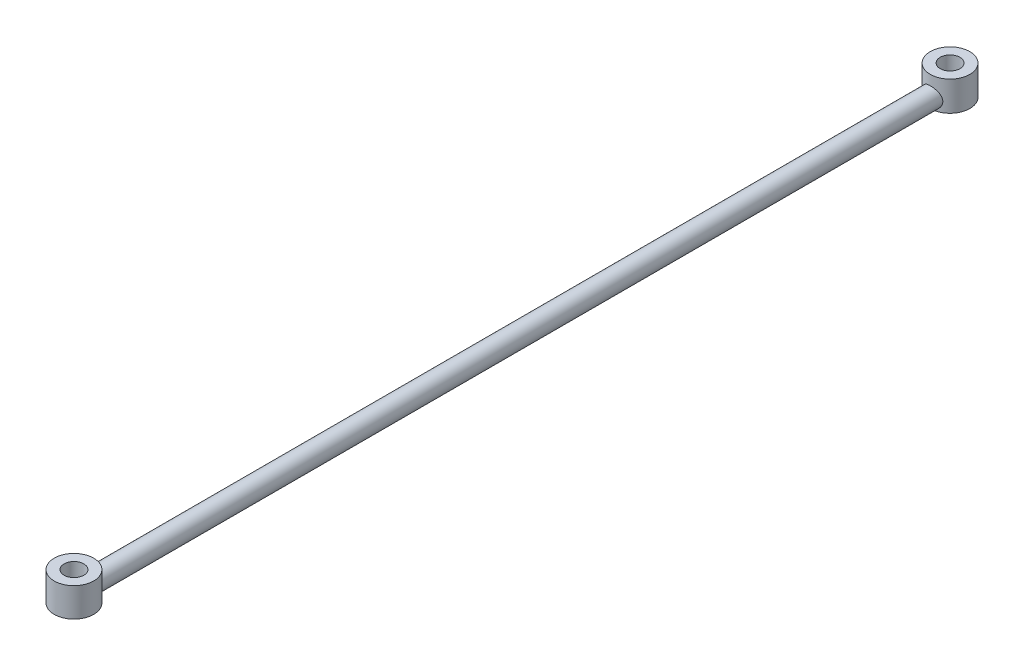
SolidWorks part; units mm, degrees
ref_plane "前视基准面" through (0, 0, 0) normal (0, 0, 1) x (1, 0, 0)
ref_plane "上视基准面" through (0, 0, 0) normal (0, 1, 0) x (1, 0, 0)
ref_plane "右视基准面" through (0, 0, 0) normal (1, 0, 0) x (0, 0, -1)
other "Configuration Table"
sketch "草图1" plane through (0, 0, 0) normal (0, 1, 0) x (1, 0, 0)
  circle A0 centre (0, 0) radius 1.5
  circle A1 centre (0, 0) radius 3
  circle A2 centre (0, -133) radius 1.5
  circle A3 centre (0, -133) radius 3
  dimension "D1" = 3
  dimension "D2" = 6
  dimension "D3" = 133
extrude "凸台-拉伸1" add sketch "草图1" along normal blind 3
ref_plane "基准面1" through (0, 0, 1.6) normal (0, 0, 1) x (1, 0, 0)
sketch "草图2" plane through (0, 0, 1.6) normal (0, 0, 1) x (1, 0, 0)
  line L0 (0, -1.65) -> (0, 1.65) construction
  line L1 (3.3, 0) -> (-3.3, 0) construction
  circle A0 centre (0, 1.5) radius 1.5
  point P0 (0, 1.5)
  dimension "D2" = 3
  dimension "D1" = 1.5
extrude "凸台-拉伸2" add sketch "草图2" along normal blind 129.8
ref_plane "基准面2" through (0, 3, 0) normal (0, 1, 0) x (1, 0, 0)
sketch "草图3" plane through (0, 3, 0) normal (0, 1, 0) x (1, 0, 0)
  circle A0 centre (0, 0) radius 1.5
  circle A1 centre (0, 0) radius 3
  dimension "D1" = 3
  dimension "D2" = 6
extrude "凸台-拉伸3" add sketch "草图3" along normal blind 1.5
ref_plane "基准面3" through (0, 3, 0) normal (0, 1, 0) x (1, 0, 0)
sketch "草图4" plane through (0, 3, 0) normal (0, 1, 0) x (1, 0, 0)
  circle A0 centre (0, -133) radius 3
  circle A1 centre (0, -133) radius 1.5
extrude "凸台-拉伸4" add sketch "草图4" along normal blind 1.4
